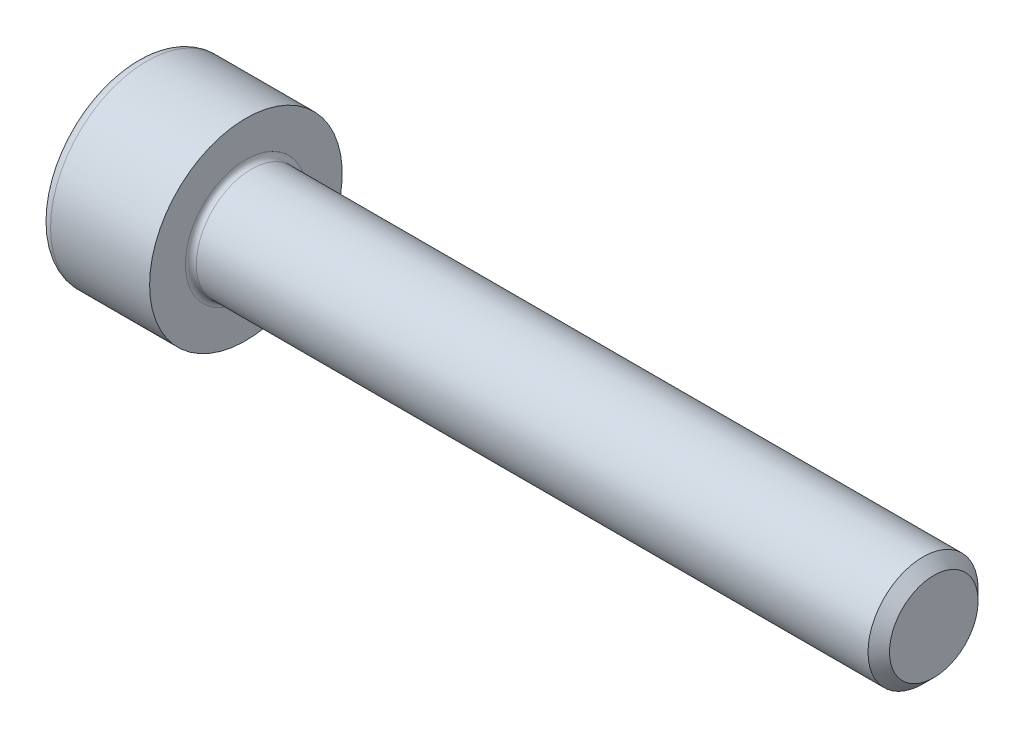
SolidWorks part; units mm, degrees
ref_plane "Plane1" through (0, 0, 0) normal (0, 0, 1) x (1, 0, 0)
ref_plane "Plane2" through (0, 0, 0) normal (0, 1, 0) x (1, 0, 0)
ref_plane "Plane3" through (0, 0, 0) normal (1, 0, 0) x (0, 0, -1)
sketch "BodySke" plane through (0, 0, 0) normal (0, 0, 1) x (1, 0, 0)
  line L0 (0, 0) -> (0, 3.5)
  line L1 (0, 3.5) -> (4, 3.5)
  line L2 (4, 3.5) -> (4, 2)
  line L3 (4, 2) -> (28.61, 2)
  line L4 (29, 1.61) -> (29, 0)
  line L5 (29, 0) -> (0, 0)
  line L6 (-31.75, 0) -> (127, 0) construction
  line L8 (29, 1.61) -> (28.61, 2)
  line L10 (29, -1.61) -> (28.61, -2) construction
  line L11 (4.7, 9.525) -> (4.7, 3.175) construction
  line L12 (4, 9.525) -> (4, 3.175) construction
  line L13 (-31, 9.525) -> (-31, 3.175) construction
  dimension "Diameter" = 4
  dimension "Head_ht" = 4
  dimension "Length" = 25
  dimension "Body_ch_ang" = 45
  dimension "Head_dia" = 7
  dimension "Minor_dia" = 3.22
  dimension "Advance" = 0.7
  dimension "Thread_nom" = 25
  dimension "Thread_length" = 60
revolve "Base-Revolve" add sketch "BodySke"
cosmetic thread "ThreadCosmetic" [suppressed]
fillet "Fillet1" radius 0.2 1 edges at (4, 0, 2)
fillet "Fillet2" radius 0.4 1 edges at (0, 0, 3.5)
sketch "Sketch2" plane through (0, 0, 0) normal (0, 0, 1) x (1, 0, 0)
  line L0 (0, 1.51) -> (2, 1.51)
  line L1 (2, 1.51) -> (2.8718, 0)
  line L2 (-31.75, 0) -> (127, 0) construction
  line L3 (2.8718, 0) -> (0, 0)
  line L4 (0, 0) -> (0, 1.51)
  line L6 (0, 0) -> (47.625, 0) construction
  dimension "D1" = 1.51
  dimension "D2" = 60
  dimension "Depth" = 2
revolve "Hex-PreBroach" cut sketch "Sketch2" angle 360 about L6
sketch "Sketch3" plane through (0, 0, 0) normal (-1, 0, 0) x (0, 0.5, 0.866)
  line L0 (0.8718, 1.51) -> (-0.8718, 1.51)
  line L1 (-0.8718, 1.51) -> (-1.7436, 0)
  line L2 (0.8718, 1.51) -> (1.7436, 0)
  line L3 (0.8718, -1.51) -> (1.7436, 0)
  line L4 (0.8718, -1.51) -> (-0.8718, -1.51)
  line L5 (-0.8718, -1.51) -> (-1.7436, 0)
  dimension "D1" = 1.51
  dimension "D2" = 1.51
  dimension "Hex_size" = 3.02
extrude "Hex" cut sketch "Sketch3" against normal blind 2
sketch "ThdSchSke" plane through (0, 0, 0) normal (0, 0, 1) x (1, 0, 0)
  line L0 (6.1, -1.61) -> (5.8269, -2)
  line L1 (6.1, -1.61) -> (6.3731, -2)
  line L2 (6.3731, -2) -> (6.3731, -2.5)
  line L3 (-3.175, 0) -> (5.1513, 0) construction
  line L4 (0, 3.1) -> (0, -3.1) construction
  line L5 (6.3731, -2.5) -> (5.8269, -2.5)
  line L6 (5.8269, -2.5) -> (5.8269, -2)
  dimension "Thread_minor" = 3.22
  dimension "Diameter" = 4
  dimension "Start" = 6.1
  dimension "SideAngle" = 55
  dimension "VeeAngle" = 70
  dimension "Overcut" = 5
revolve "ThreadSchematic" [suppressed] cut sketch "ThdSchSke" angle 360 about L3
pattern_linear "ThdSchPat" [suppressed]
equation "\"D2@Sketch3\" = \"Hex_size@Sketch3\" / 2"
equation "\"D1@Sketch3\" = \"Hex_size@Sketch3\" / 2"
equation "\"D1@Sketch2\" = \"Hex_size@Sketch3\" / 2"
equation "\"Thread_minor@ThreadCosmetic\"  =  \"Minor_dia@BodySke\""
equation "\"Depth@Sketch2\" =  \"Key_eng@Hex\""
equation "\"Thread_length@ThreadCosmetic\" = ((sgn( (\"Length@BodySke\" - \"Advance@BodySke\" * 3.0) - \"Thread_nom@BodySke\" )-1)*( (\"Length@BodySke\" - \"Advance@BodySke\" * 3.0) - \"Thread_nom@BodySke\" ))/-2+ \"Thread_nom@BodySke\""
equation "\"Thread_minor@ThdSchSke\" = \"Minor_dia@BodySke\""
equation "\"Diameter@ThdSchSke\" = \"Diameter@BodySke\""
equation "\"Overcut@ThdSchSke\" = \"Diameter@BodySke\" * 1.25"
equation "\"Start@ThdSchSke\" = \"Head_ht@BodySke\" + \"Length@BodySke\" - \"Thread_length@ThreadCosmetic\"  '---Non-countersunk---"
equation "\"Num_threads@ThdSchPat\" = int( \"Thread_length@ThreadCosmetic\" / \"Advance@BodySke\" + 0.999 )  + 1"
equation "\"Advance@ThdSchPat\" = \"Thread_length@ThreadCosmetic\" /  (\"Num_threads@ThdSchPat\" - 1) 'relax it"
equation "\"Num_threads@ThdSchPat\" = \"Num_threads@ThdSchPat\" - sgn( \"Num_threads@ThdSchPat\" - 1) '---chamfered tips only---"
